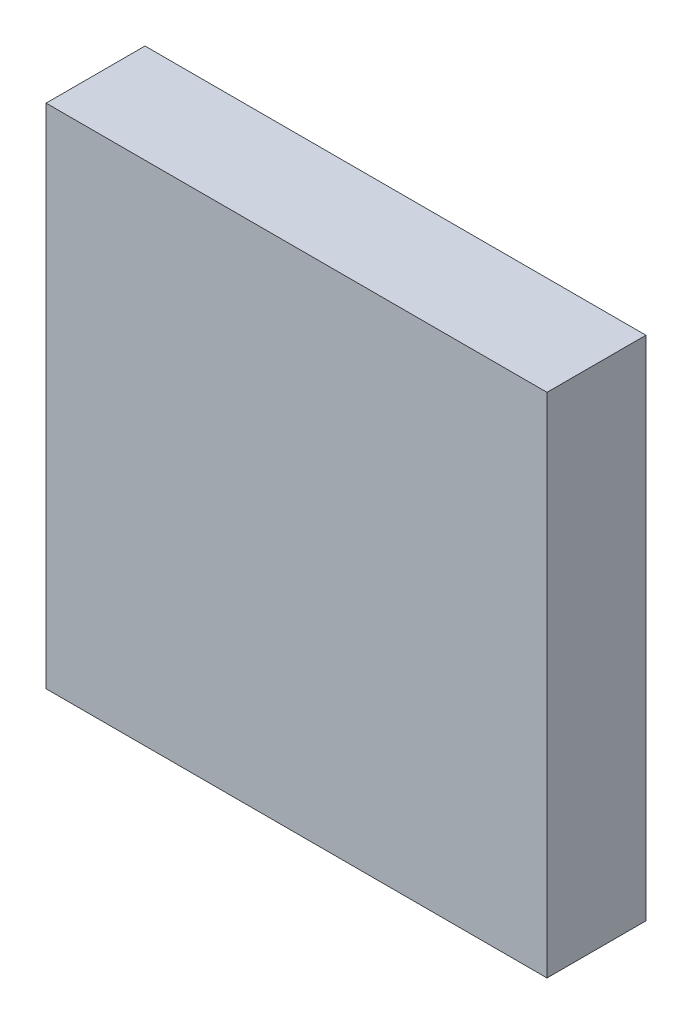
SolidWorks part; units mm, degrees
ref_plane "Front Plane" through (0, 0, 0) normal (0, 0, 1) x (1, 0, 0)
ref_plane "Top Plane" through (0, 0, 0) normal (0, 1, 0) x (1, 0, 0)
ref_plane "Right Plane" through (0, 0, 0) normal (1, 0, 0) x (0, 0, -1)
sketch "Sketch1" plane through (0, 0, 0) normal (0, 0, 1) x (1, 0, 0)
  line L0 (-4.0513, -4.1021) -> (4.0513, -4.1021)
  line L1 (4.0513, -4.1021) -> (4.0513, 4.1021)
  line L2 (4.0513, 4.1021) -> (-4.0513, 4.1021)
  line L3 (-4.0513, 4.1021) -> (-4.0513, -4.1021)
extrude "Component_Outline" add sketch "Sketch1" along normal blind 1.5999 separate body
sketch3d "3DSketch1"
  line L0 (0, 0, 0) -> (1, 0, 0)
  line L1 (0, 0, 0) -> (0, 1, 0)
  line L2 (0, 0, 0) -> (0, 0, 1)
  point P0 (0, 0, 0)
